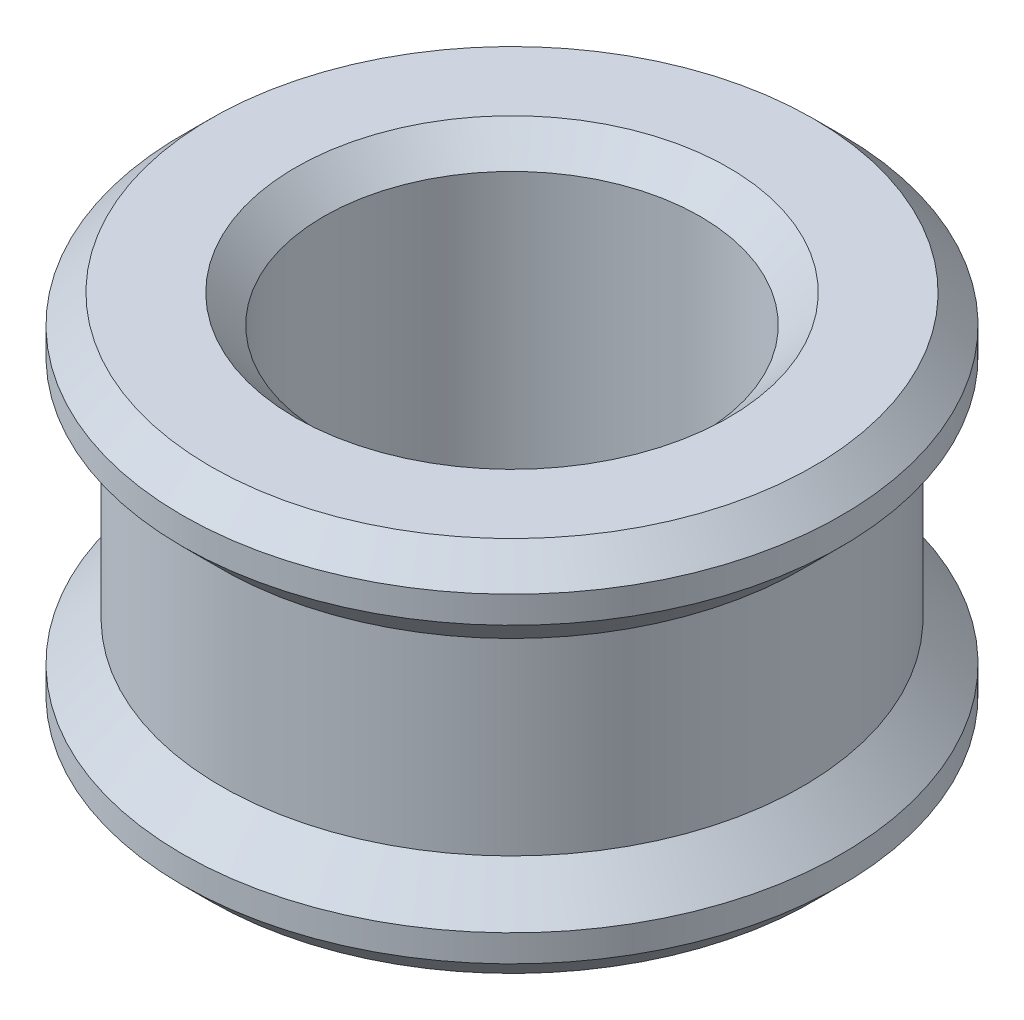
SolidWorks part; units mm, degrees
ref_plane "Front Plane" through (0, 0, 0) normal (0, 0, 1) x (1, 0, 0)
ref_plane "Top Plane" through (0, 0, 0) normal (0, 1, 0) x (1, 0, 0)
ref_plane "Right Plane" through (0, 0, 0) normal (1, 0, 0) x (0, 0, -1)
sketch "Sketch2" plane through (0, 0, 0) normal (0, 0, 1) x (1, 0, 0)
  line L0 (0, 0) -> (0, 31.2573) construction
  line L1 (2, 0) -> (2, 4)
  line L2 (2, 4) -> (3.5, 4)
  line L3 (3.5, 4) -> (3.5, 3.4142)
  line L4 (3.5, 3.4142) -> (3.0858, 3)
  line L5 (3.0858, 3) -> (3.0858, 1)
  line L6 (3.0858, 1) -> (3.5, 0.5858)
  line L7 (3.5, 0.5858) -> (3.5, 0)
  line L8 (3.5, 0) -> (2, 0)
  point P11 (14.6782, 1.8177)
  point P12 (0, 0)
  dimension "D1" = 225
  dimension "D2" = 2
  dimension "D3" = 2
  dimension "D4" = 1.5
  dimension "D5" = 4
revolve "Revolve1" add sketch "Sketch2" angle 360 about L0
chamfer "Chamfer1" distance 0.3 angle 45 4 edges at (0, 4, -2) (0, 0, -2) (0, 0, -3.5) (0, 4, -3.5)
